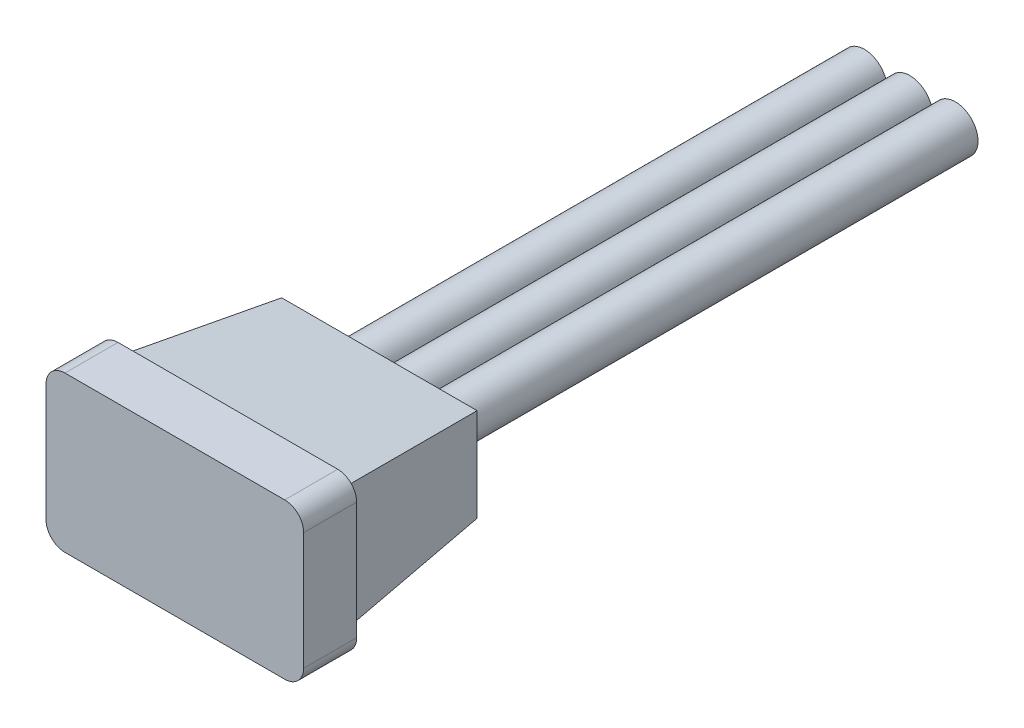
SolidWorks part; units mm, degrees
ref_plane "Front Plane" through (0, 0, 0) normal (0, 0, 1) x (1, 0, 0)
ref_plane "Top Plane" through (0, 0, 0) normal (0, 1, 0) x (1, 0, 0)
ref_plane "Right Plane" through (0, 0, 0) normal (1, 0, 0) x (0, 0, -1)
sketch "BaseS" plane through (0, 0, 0) normal (0, 0, 1) x (1, 0, 0)
  line L0 (-3.4, 2.05) -> (3.4, 2.05)
  line L1 (-3.4, 2.05) -> (-3.4, -2.05)
  line L2 (-3.4, -2.05) -> (3.4, -2.05)
  line L3 (3.4, 2.05) -> (3.4, -2.05)
  line L4 (-3.4, 2.05) -> (3.4, -2.05) construction
  line L5 (-3.4, -2.05) -> (3.4, 2.05) construction
  point P0 (0, 0)
  dimension "D1" = 6.8
  dimension "D2" = 4.1
extrude "BASE" add sketch "BaseS" against normal blind 1.4
sketch "ExtendedBodyS" plane through (0, 0, -1.4) normal (0, 0, -1) x (-1, 0, 0)
  line L0 (-3, 1.65) -> (-3, -1.65)
  line L1 (-3, -1.65) -> (3, -1.65)
  line L2 (3, -1.65) -> (3, 1.65)
  line L3 (3, 1.65) -> (-3, 1.65)
  line L4 (-3.4, 2.05) -> (-3.4, -2.05)
  line L5 (-3.4, -2.05) -> (3.4, -2.05)
  line L6 (3.4, -2.05) -> (3.4, 2.05)
  line L7 (3.4, 2.05) -> (-3.4, 2.05)
  line L8 (-3.4, 2.05) -> (-3.4, -2.05) construction
  line L9 (-3.4, -2.05) -> (3.4, -2.05) construction
  line L10 (3.4, -2.05) -> (3.4, 2.05) construction
  line L11 (3.4, 2.05) -> (-3.4, 2.05) construction
  dimension "D1" = 0
  dimension "D2" = 0.4
extrude "EXTENDED BODY" add sketch "ExtendedBodyS" along normal blind 4 draft 6
sketch "PositiveS" plane through (0, 0, -5.4) normal (0, 0, -1) x (-1, 0, 0)
  circle A0 centre (0, 0) radius 0.6
  dimension "D1" = 1.2
extrude "POSITIVE" add sketch "PositiveS" along normal blind 14
sketch "SignalS" plane through (0, 0, -5.4) normal (0, 0, -1) x (-1, 0, 0)
  line L0 (0, 0) -> (1.2, 0) construction
  circle A0 centre (1.2, 0) radius 0.6
  circle A1 centre (0, 0) radius 0.6 construction
extrude "SIGNAL" add sketch "SignalS" along normal up to surface (14 mm away) separate body up to face at (-0.6, 0, -19.4)
sketch "NegativeS" plane through (0, 0, -5.4) normal (0, 0, -1) x (-1, 0, 0)
  line L0 (0, 0) -> (-1.2, 0) construction
  circle A0 centre (-1.2, 0) radius 0.6
  circle A1 centre (0, 0) radius 0.6 construction
extrude "NEGATIVE" add sketch "NegativeS" along normal up to surface (14 mm away) separate body up to face at (-0.6, 0, -19.4)
fillet "BASE F" radius 0.5 4 edges at (-3.4, -2.05, -0.7) (-3.4, 2.05, -0.7) (3.4, -2.05, -0.7) (3.4, 2.05, -0.7)
